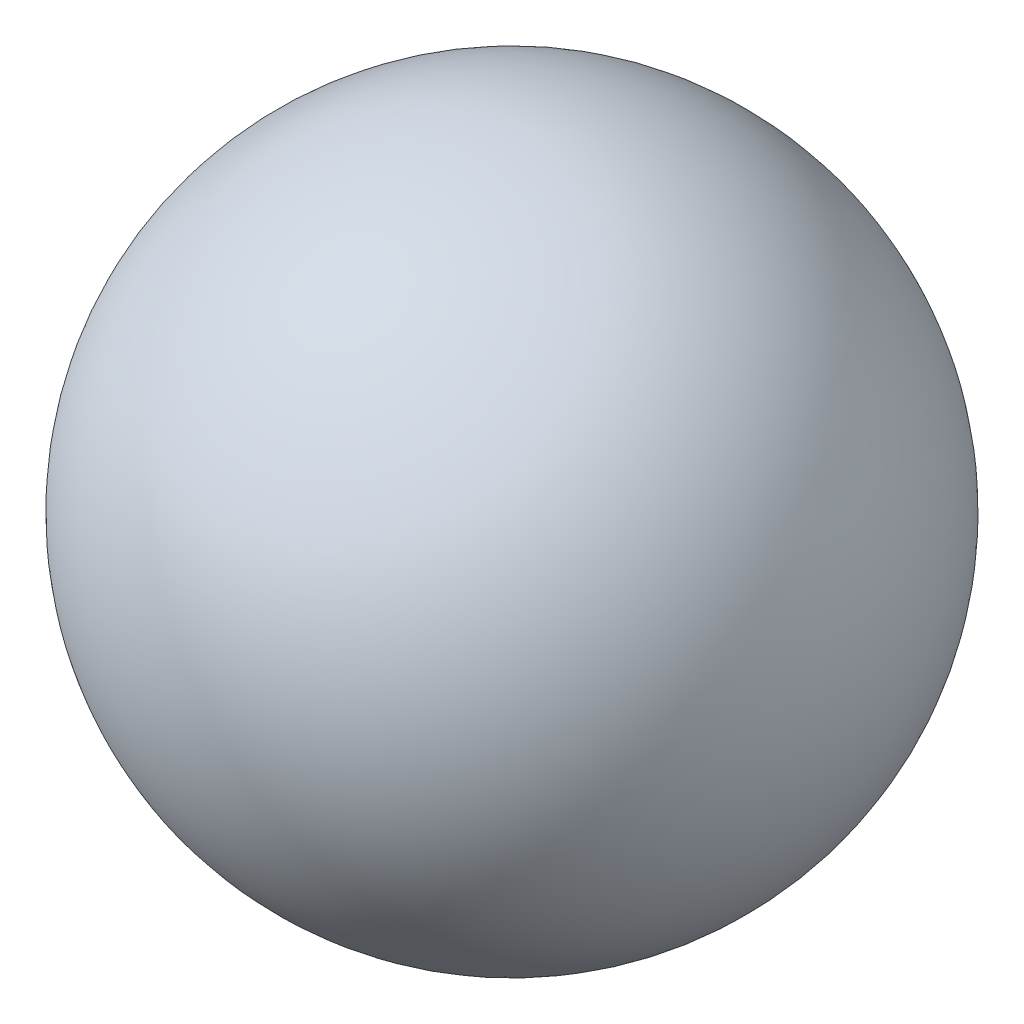
SolidWorks part; units mm, degrees
ref_plane "Front Plane" through (0, 0, 0) normal (0, 0, 1) x (1, 0, 0)
ref_plane "Top Plane" through (0, 0, 0) normal (0, 1, 0) x (1, 0, 0)
ref_plane "Right Plane" through (0, 0, 0) normal (1, 0, 0) x (0, 0, -1)
sketch "Sketch2" plane through (0, 0, 0) normal (0, 1, 0) x (1, 0, 0)
  line L0 (-201.3352, 109.6036) -> (-201.3352, 42.9036)
  arc A0 (-201.3352, 109.6036) -> (-201.3352, 42.9036) centre (-201.3352, 76.2536) ccw
  dimension "D1" = 66.7
revolve "Revolve1" add sketch "Sketch2" angle 360 about L0
